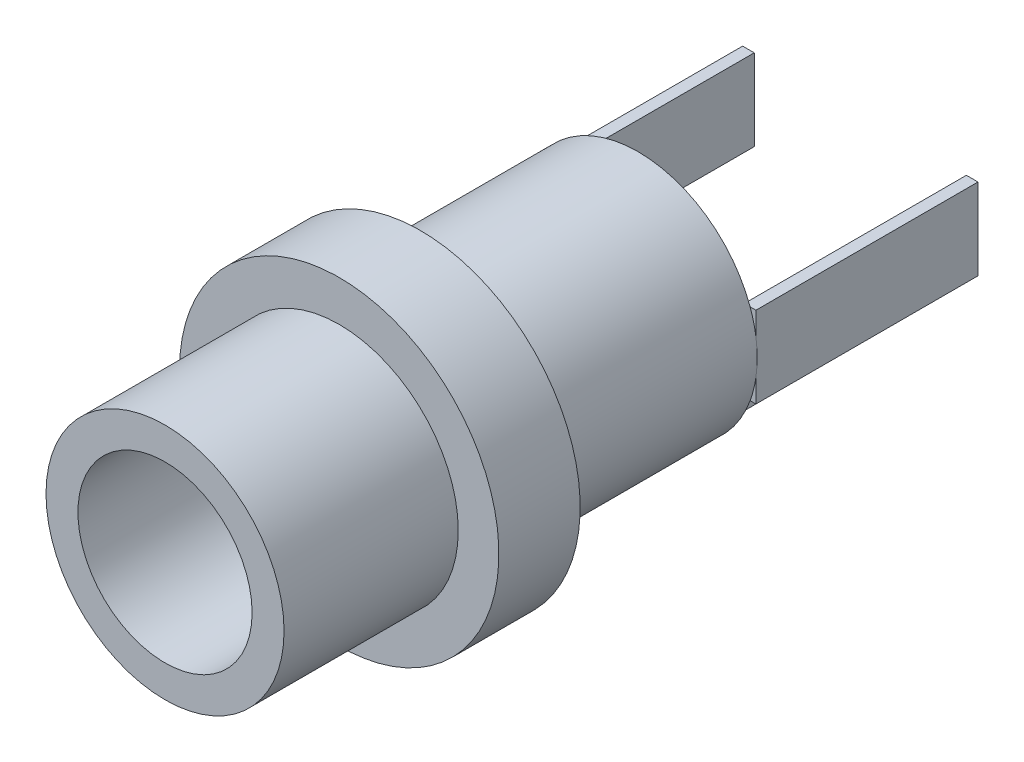
SolidWorks part; units mm, degrees
ref_plane "Front Plane" through (0, 0, 0) normal (0, 0, 1) x (1, 0, 0)
ref_plane "Top Plane" through (0, 0, 0) normal (0, 1, 0) x (1, 0, 0)
ref_plane "Right Plane" through (0, 0, 0) normal (1, 0, 0) x (0, 0, -1)
sketch "Sketch1" plane through (0, 0, 0) normal (0, 0, 1) x (1, 0, 0)
  circle A0 centre (0, 0) radius 4.1
  circle A1 centre (0, 0) radius 3
  dimension "D1" = 8.2
  dimension "D2" = 6
extrude "Boss-Extrude1" add sketch "Sketch1" against normal blind 6
sketch "Sketch2" plane through (0, 0, -6) normal (0, 0, -1) x (-1, 0, 0)
  circle A0 centre (0, 0) radius 5.5
  dimension "D1" = 11
extrude "Boss-Extrude2" add sketch "Sketch2" along normal blind 2.8
sketch "Sketch3" plane through (0, 0, -8.8) normal (0, 0, -1) x (-1, 0, 0)
  circle A0 centre (0, 0) radius 4.1
  dimension "D1" = 8.2
extrude "Boss-Extrude3" add sketch "Sketch3" along normal blind 7.5
sketch "Sketch4" plane through (0, 0, -16.3) normal (0, 0, -1) x (-1, 0, 0)
  line L0 (-3.8536, 1.4) -> (-3.8536, -1.4)
  line L1 (-1.4, -3.8536) -> (1.4, -3.8536)
  line L2 (3.8536, 1.4) -> (3.8536, -1.4)
  circle A0 centre (0, 0) radius 4.1 construction
  circle A1 centre (0, 0) radius 4.1 construction
  point P6 (-3.8536, 0)
  point P7 (3.8536, 0)
  point P9 (0, -3.8536)
  dimension "D1" = 2.8
extrude "Extrude-Thin1" add sketch "Sketch4" along normal blind 7.65 thin thin type mid plane wall 0.4
